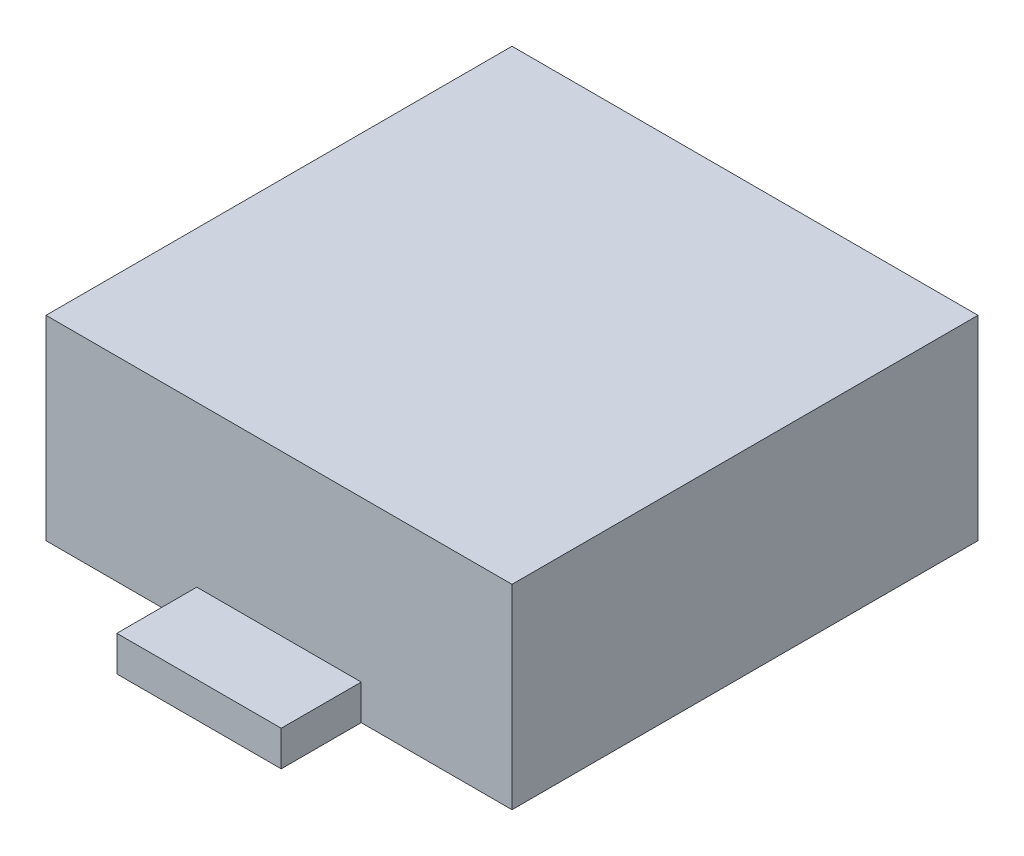
SolidWorks part; units mm, degrees
ref_plane "Front Plane" through (0, 0, 0) normal (0, 0, 1) x (1, 0, 0)
ref_plane "Top Plane" through (0, 0, 0) normal (0, 1, 0) x (1, 0, 0)
ref_plane "Right Plane" through (0, 0, 0) normal (1, 0, 0) x (0, 0, -1)
sketch "Sketch1" plane through (0, 0, 0) normal (0, 1, 0) x (1, 0, 0)
  line L1 (0, 0) -> (74, 0)
  line L2 (0, 0) -> (0, 74)
  line L3 (0, 74) -> (74, 74)
  line L4 (74, 0) -> (74, 74)
  dimension "D1" = 74
  dimension "D2" = 74
extrude "Boss-Extrude1" add sketch "Sketch1" along normal blind 31
sketch "Sketch2" plane through (0, 0, 0) normal (0, 0, 1) x (1, 0, 0)
  line L0 (0, 0) -> (74, 0) construction
  line L1 (23.9467, 5.5886) -> (50.0533, 5.5886)
  line L2 (23.9467, 5.5886) -> (23.9467, 0)
  line L3 (23.9467, 0) -> (50.0533, 0)
  line L4 (50.0533, 5.5886) -> (50.0533, 0)
  point P6 (37, 0)
  point P7 (37, 0)
extrude "Boss-Extrude2" add sketch "Sketch2" along normal blind 12.7
